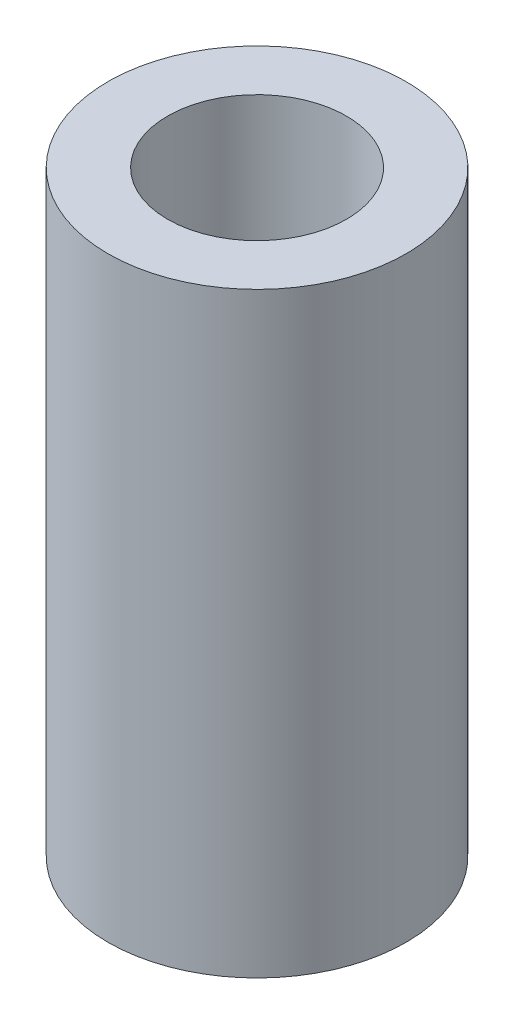
SolidWorks part; units mm, degrees
material "1060 Alloy"
ref_plane "Front Plane" through (0, 0, 0) normal (0, 0, 1) x (1, 0, 0)
ref_plane "Top Plane" through (0, 0, 0) normal (0, 1, 0) x (1, 0, 0)
ref_plane "Right Plane" through (0, 0, 0) normal (1, 0, 0) x (0, 0, -1)
sketch "Sketch1" plane through (0, 0, 0) normal (0, 1, 0) x (1, 0, 0)
  circle A0 centre (0, 0) radius 0.5
  circle A1 centre (0, 0) radius 1
  dimension "D1" = 1
  dimension "D2" = 2
extrude "Boss-Extrude1" add sketch "Sketch1" along normal blind 1
sketch "Sketch2" plane through (0, 1, 0) normal (0, 1, 0) x (1, 0, 0)
  circle A0 centre (0, 0) radius 1
  dimension "D1" = 2
extrude "Boss-Extrude2" add sketch "Sketch2" along normal blind 3
hole_wizard "M1 Clearance Hole1" positions "Sketch3" profile "Sketch4" hole size "M1" standard "AS"
sketch "Sketch3" plane through (0, 4, 0) normal (0, 1, 0) x (1, 0, 0)
  point P0 (0, 0)
sketch "Sketch4" plane through (0, 4, 0) normal (1, 0, 0) x (0, 0, 1)
  line L0 (0, 0) -> (0, 2.3605)
  line L1 (0, 2.3605) -> (0.6, 2)
  line L2 (0.6, 2) -> (0.6, 0)
  line L5 (0.6, 0) -> (0, 0)
  line L10 (0, 2.3605) -> (-0.6, 2) construction
  line L11 (0, -6.35) -> (0, 107.95) construction
  dimension "Hole Dia." = 1.2
  dimension "Hole Depth" = 2
  dimension "Drill Angle" = 118
